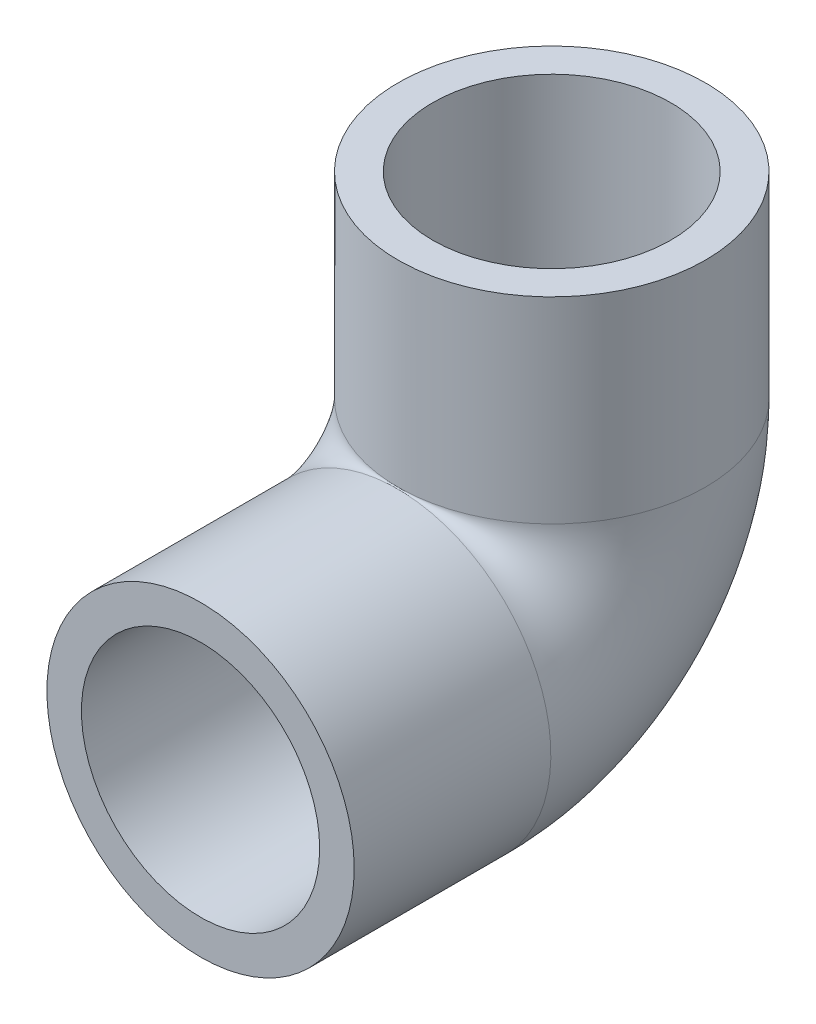
SolidWorks part; units mm, degrees
ref_plane "Front Plane" through (0, 0, 0) normal (0, 0, 1) x (1, 0, 0)
ref_plane "Top Plane" through (0, 0, 0) normal (0, 1, 0) x (1, 0, 0)
ref_plane "Right Plane" through (0, 0, 0) normal (1, 0, 0) x (0, 0, -1)
sketch "Sketch1" plane through (0, 0, 0) normal (0, 0, 1) x (1, 0, 0)
  circle A0 centre (0, 0) radius 13.8906
  circle A1 centre (0, 0) radius 8.89
  dimension "D1" = 27.7813
  dimension "D2" = 17.78
sketch "Sketch2" plane through (0, 0, 0) normal (1, 0, 0) x (0, 0, -1)
  line L0 (0, 0) -> (17.78, 0)
  line L1 (31.75, 13.97) -> (31.75, 31.75)
  arc A0 (17.78, 0) -> (31.75, 13.97) centre (17.78, 13.97) ccw
  point P6 (31.75, 0)
  dimension "D3" = 13.97
  dimension "D1" = 31.75
  dimension "D2" = 31.75
sweep "Sweep1" add profiles "Sketch1" path "Sketch2"
sketch "Sketch3" plane through (0, 0, 0) normal (0, 0, 1) x (1, 0, 0)
  circle A0 centre (0, 0) radius 10.7696
  dimension "D1" = 21.5392
extrude "Cut-Extrude1" cut sketch "Sketch3" against normal blind 19.05
sketch "Sketch4" plane through (0, 31.75, 0) normal (0, 1, 0) x (1, 0, 0)
  circle A0 centre (0, 31.75) radius 10.7696
  dimension "D1" = 21.5392
extrude "Cut-Extrude2" cut sketch "Sketch4" against normal blind 19.05
